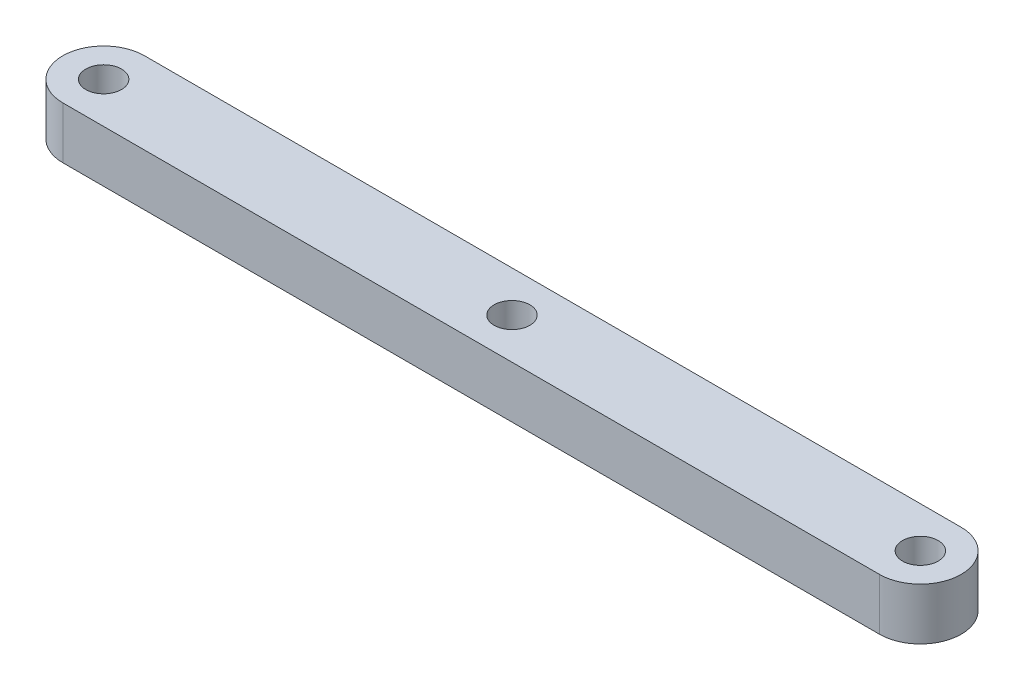
SolidWorks part; units mm, degrees
ref_plane "Front Plane" through (0, 0, 0) normal (0, 0, 1) x (1, 0, 0)
ref_plane "Top Plane" through (0, 0, 0) normal (0, 1, 0) x (1, 0, 0)
ref_plane "Right Plane" through (0, 0, 0) normal (1, 0, 0) x (0, 0, -1)
sketch "Sketch1" plane through (0, 0, 0) normal (0, 1, 0) x (1, 0, 0)
  line L1 (-10.0218, 6.5241) -> (39.9782, 6.5241)
  line L4 (-10.0218, 1.5241) -> (39.9782, 1.5241)
  circle A0 centre (-10.0218, 4.0241) radius 1.0922
  circle A1 centre (39.9782, 4.0241) radius 1.0922
  circle A5 centre (14.9782, 4.0241) radius 1.0922
  arc A11 (-10.0218, 6.5241) -> (-10.0218, 1.5241) centre (-10.0218, 4.0241) ccw
  arc A12 (39.9782, 1.5241) -> (39.9782, 6.5241) centre (39.9782, 4.0241) ccw
  dimension "D2" = 2.1844
  dimension "D5" = 2.1844
  dimension "D6" = 2.5
  dimension "D1" = 2.1844
extrude "Boss-Extrude1" add sketch "Sketch1" along normal blind 3.175
